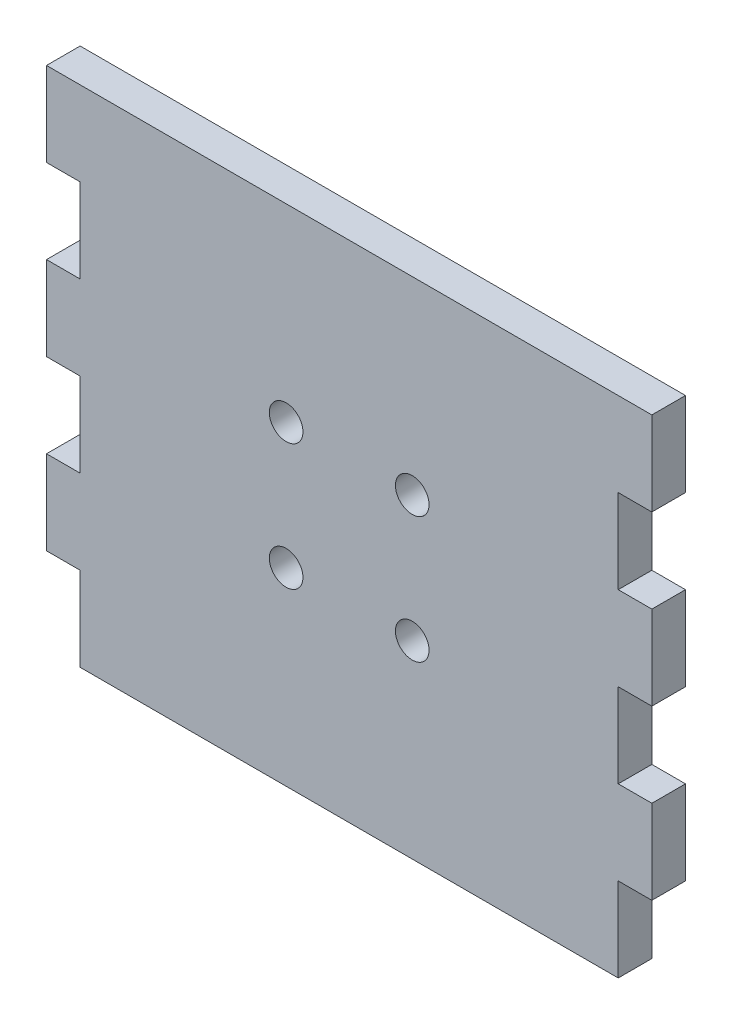
SolidWorks part; units mm, degrees
material "1060 Alloy"
ref_plane "Front Plane" through (0, 0, 0) normal (0, 0, 1) x (1, 0, 0)
ref_plane "Top Plane" through (0, 0, 0) normal (0, 1, 0) x (1, 0, 0)
ref_plane "Right Plane" through (0, 0, 0) normal (1, 0, 0) x (0, 0, -1)
sketch "Sketch1" plane through (0, 0, 0) normal (0, 0, 1) x (1, 0, 0)
  line L0 (36, 20) -> (32, 20)
  line L1 (-36, 30) -> (36, 30)
  line L2 (-36, 30) -> (-36, 20)
  line L3 (-32, -30) -> (32, -30)
  line L4 (36, 30) -> (36, 20)
  line L5 (-36, 30) -> (36, -30) construction
  line L6 (-36, -30) -> (36, 30) construction
  line L11 (-7.5, 7.5) -> (6.0858, -6.0858) construction
  line L12 (-7.5, -7.5) -> (7.5, 7.5) construction
  line L13 (32, 20) -> (32, 10)
  line L14 (32, 10) -> (36, 10)
  line L15 (36, 0) -> (32, 0)
  line L16 (32, 0) -> (32, -10)
  line L17 (32, -10) -> (36, -10)
  line L18 (36, -20) -> (32, -20)
  line L19 (32, -20) -> (32, -30)
  line L20 (36, -10) -> (36, -20)
  line L21 (36, 10) -> (36, 0)
  line L22 (-36, 20) -> (-32, 20)
  line L23 (-32, 20) -> (-32, 10)
  line L24 (-32, 10) -> (-36, 10)
  line L25 (-36, 0) -> (-32, 0)
  line L26 (-32, 0) -> (-32, -10)
  line L27 (-32, -10) -> (-36, -10)
  line L28 (-36, -20) -> (-32, -20)
  line L29 (-32, -20) -> (-32, -30)
  line L30 (-36, 10) -> (-36, 0)
  line L31 (-36, -10) -> (-36, -20)
  circle A0 centre (-7.5, 7.5) radius 2
  circle A1 centre (-7.5, -7.5) radius 2
  circle A2 centre (7.5, -7.5) radius 2
  circle A3 centre (7.5, 7.5) radius 2
  point P0 (0, 0)
  point P6 (0, 0)
  dimension "D5" = 4
  dimension "D6" = 4
  dimension "D7" = 4
  dimension "D8" = 4
  dimension "D1" = 72
  dimension "D2" = 60
  dimension "D3" = 15
  dimension "D4" = 15
  dimension "D9" = 10
  dimension "D10" = 10
  dimension "D11" = 10
  dimension "D12" = 10
  dimension "D13" = 10
  dimension "D14" = 10
  dimension "D15" = 4
extrude "Boss-Extrude1" add sketch "Sketch1" along normal blind 4
